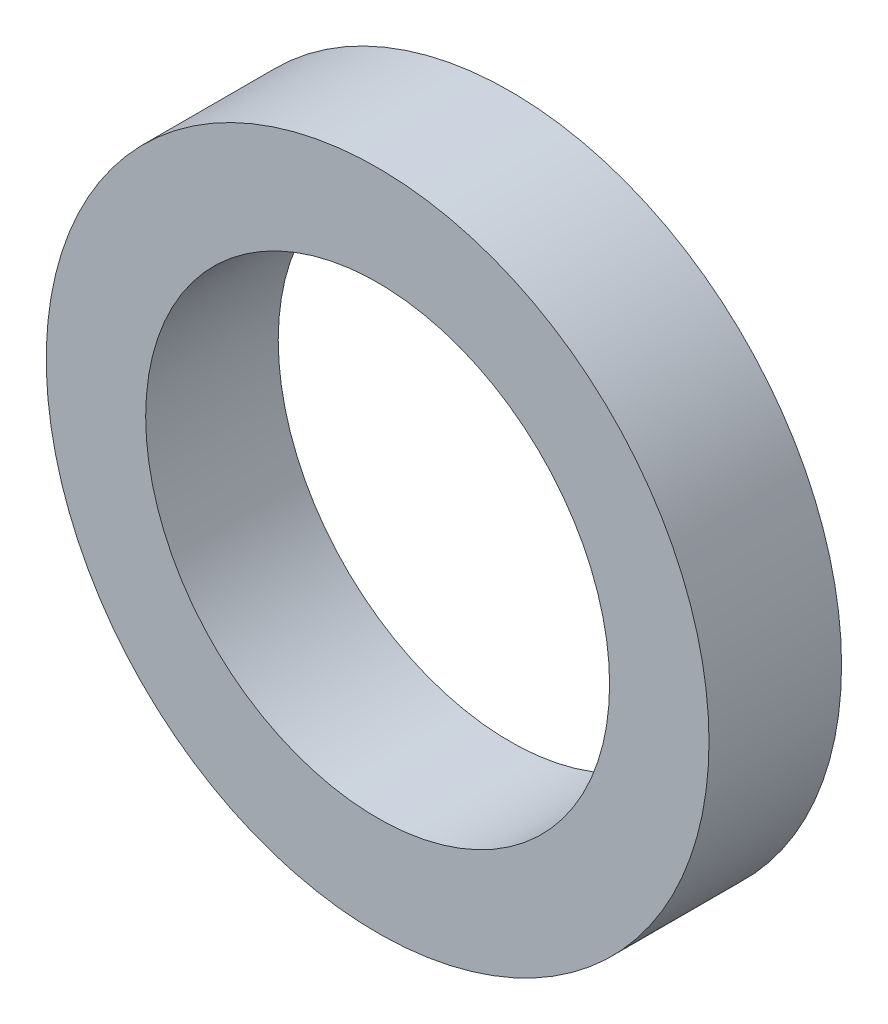
SolidWorks part; units mm, degrees
ref_plane "Alzado" through (0, 0, 0) normal (0, 0, 1) x (1, 0, 0)
ref_plane "Planta" through (0, 0, 0) normal (0, 1, 0) x (1, 0, 0)
ref_plane "Vista lateral" through (0, 0, 0) normal (1, 0, 0) x (0, 0, -1)
sketch "Croquis4" plane through (0, 0, 0) normal (0, 0, 1) x (1, 0, 0)
  circle A0 centre (0, 0) radius 35
  dimension "D1" = 70
extrude "Saliente-Extruir2" add sketch "Croquis4" along normal blind 14
sketch "Croquis5" plane through (0, 0, 0) normal (0, 0, 1) x (1, 0, 0)
  circle A1 centre (0, 0) radius 24.5
  dimension "D1" = 49
extrude "Cortar-Extruir2" cut sketch "Croquis5" along normal blind 14
